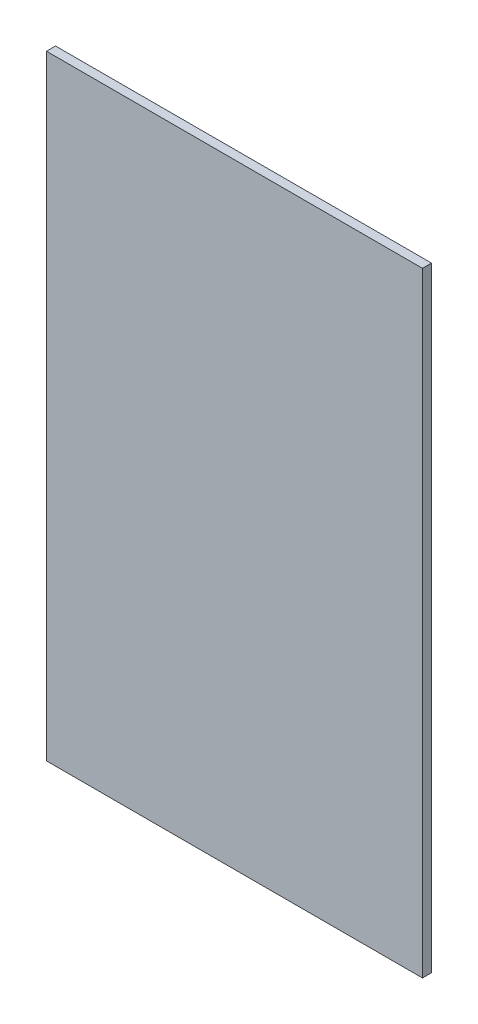
SolidWorks part; units mm, degrees
material "PC High Viscosity"
ref_plane "Front Plane" through (0, 0, 0) normal (0, 0, 1) x (1, 0, 0)
ref_plane "Top Plane" through (0, 0, 0) normal (0, 1, 0) x (1, 0, 0)
ref_plane "Right Plane" through (0, 0, 0) normal (1, 0, 0) x (0, 0, -1)
sketch "Sketch1" plane through (0, 0, 0) normal (0, 0, 1) x (1, 0, 0)
  line L1 (-104, -200) -> (104, -200)
  line L2 (-104, -200) -> (-104, 200)
  line L3 (-104, 200) -> (104, 200)
  line L4 (104, -200) -> (104, 200)
  line L5 (-104, -200) -> (104, 200) construction
  line L6 (-104, 200) -> (104, -200) construction
  point P0 (0, 0)
  dimension "D1" = 208
  dimension "D2" = 400
extrude "Boss-Extrude1" add sketch "Sketch1" along normal mid plane 5
sketch "Sketch2" plane through (0, 0, 2.5) normal (0, 0, 1) x (1, 0, 0)
  line L0 (106, 140) -> (104, 140) construction
  line L1 (-155.214, 211.8255) -> (203.9552, 211.8255)
  line L2 (-155.214, 211.8255) -> (-155.214, 140)
  line L3 (-155.214, 140) -> (203.9552, 140)
  line L4 (203.9552, 211.8255) -> (203.9552, 140)
extrude "Cut-Extrude1" cut sketch "Sketch2" against normal through all
